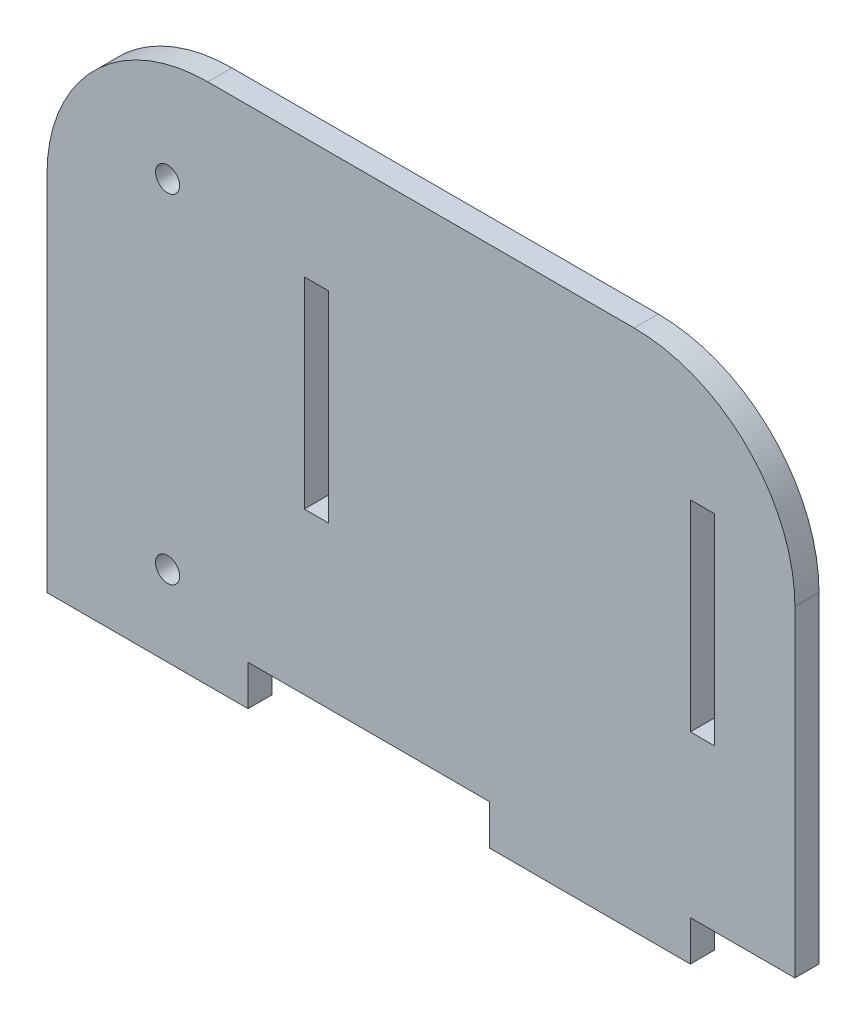
SolidWorks part; units mm, degrees
ref_plane "Plano frontal" through (0, 0, 0) normal (0, 0, 1) x (1, 0, 0)
ref_plane "Plano superior" through (0, 0, 0) normal (0, 1, 0) x (1, 0, 0)
ref_plane "Plano direito" through (0, 0, 0) normal (1, 0, 0) x (0, 0, -1)
sketch "Esboço1" plane through (0, 0, 0) normal (0, 0, 1) x (1, 0, 0)
  line L0 (43.0401, -11.3817) -> (56.0401, -11.3817)
  line L1 (-16.9599, 48.6183) -> (36.0401, 48.6183)
  line L2 (-36.9599, 28.6183) -> (-36.9599, -1.3817)
  line L3 (-11.9599, -11.3817) -> (18.0401, -11.3817)
  line L4 (56.0401, 28.6183) -> (56.0401, -11.3817)
  line L6 (-36.9599, -1.3817) -> (-36.9599, -16.3817)
  line L7 (-36.9599, -16.3817) -> (-11.9599, -16.3817)
  line L8 (-11.9599, -11.3817) -> (-11.9599, -16.3817)
  line L10 (18.0401, -11.3817) -> (18.0401, -16.3817)
  line L11 (18.0401, -16.3817) -> (43.0401, -16.3817)
  line L12 (43.0401, -11.3817) -> (43.0401, -16.3817)
  arc A0 (36.0401, 48.6183) -> (56.0401, 28.6183) centre (36.0401, 28.6183) cw
  arc A1 (-16.9599, 48.6183) -> (-36.9599, 28.6183) centre (-16.9599, 28.6183) ccw
  point P13 (56.0401, 48.6183)
  point P16 (-36.9599, 48.6183)
  dimension "D8" = 20
  dimension "D1" = 93
  dimension "D2" = 5
  dimension "D3" = 25
  dimension "D4" = 30
  dimension "D5" = 25
  dimension "D6" = 5
  dimension "D7" = 60
extrude "Ressalto-extrusão1" add sketch "Esboço1" along normal blind 3
sketch "Esboço2" plane through (0, 0, 0) normal (0, 0, -1) x (-1, 0, 0)
  line L0 (36.9599, 28.6183) -> (36.9599, -16.3817) construction
  line L2 (36.9599, -16.3817) -> (11.9599, -16.3817) construction
  circle A0 centre (21.9599, 35.6683) radius 1.5
  circle A1 centre (21.9599, -6.3817) radius 1.5
  point P10 (24.4599, -16.3817)
  dimension "D1" = 3
  dimension "D2" = 3
  dimension "D3" = 15
  dimension "D4" = 10
  dimension "D5" = 15
  dimension "D6" = 42.05
extrude "Corte-extrusão1" cut sketch "Esboço2" against normal blind 10
sketch "Esboço3" plane through (0, 0, 3) normal (0, 0, 1) x (1, 0, 0)
  line L0 (36.0401, 48.6183) -> (-16.9599, 48.6183) construction
  line L1 (-4.9599, 33.6183) -> (-1.9599, 33.6183)
  line L2 (-4.9599, 33.6183) -> (-4.9599, 8.6183)
  line L3 (-4.9599, 8.6183) -> (-1.9599, 8.6183)
  line L4 (-1.9599, 33.6183) -> (-1.9599, 8.6183)
  line L5 (43.0401, 33.6183) -> (46.0401, 33.6183)
  line L6 (43.0401, 33.6183) -> (43.0401, 8.6183)
  line L7 (43.0401, 8.6183) -> (46.0401, 8.6183)
  line L8 (46.0401, 33.6183) -> (46.0401, 8.6183)
  line L9 (56.0401, -11.3817) -> (56.0401, 28.6183) construction
  point P10 (9.5401, 48.6183)
  dimension "D1" = 15
  dimension "D2" = 25
  dimension "D3" = 45
  dimension "D4" = 10
  dimension "D5" = 3
  dimension "D6" = 3
  dimension "D7" = 25
  dimension "D8" = 15
extrude "Corte-extrusão2" cut sketch "Esboço3" against normal blind 10
